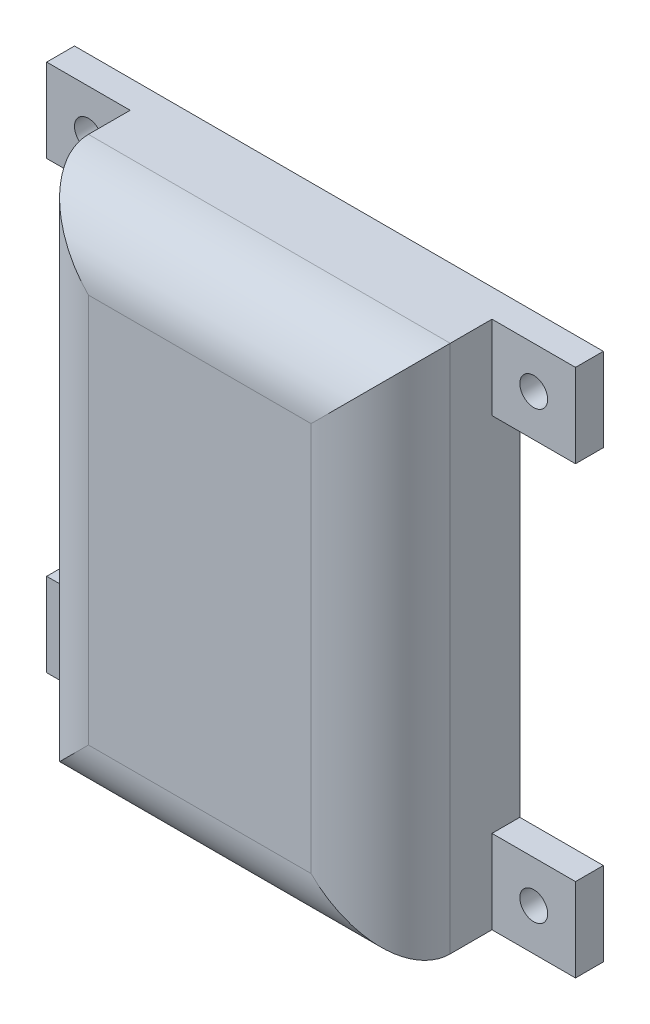
SolidWorks part; units mm, degrees
ref_plane "正面" through (0, 0, 0) normal (0, 0, 1) x (1, 0, 0)
ref_plane "平面" through (0, 0, 0) normal (0, 1, 0) x (1, 0, 0)
ref_plane "右側面" through (0, 0, 0) normal (1, 0, 0) x (0, 0, -1)
sketch "ｽｹｯﾁ1" plane through (0, 0, 0) normal (0, 0, 1) x (1, 0, 0)
  line L1 (13, -19) -> (-13, -19)
  line L2 (13, -19) -> (13, 19)
  line L3 (13, 19) -> (-13, 19)
  line L4 (-13, -19) -> (-13, 19)
  line L5 (13, -19) -> (-13, 19) construction
  line L6 (13, 19) -> (-13, -19) construction
  point P0 (0, 0)
  dimension "D1" = 38
  dimension "D2" = 26
extrude "ﾎﾞｽ - 押し出し1" add sketch "ｽｹｯﾁ1" along normal blind 10
sketch "ｽｹｯﾁ2" plane through (0, 0, 0) normal (0, 0, 1) x (1, 0, 0)
  line L1 (11, -17) -> (-11, -17)
  line L2 (11, -17) -> (11, 17)
  line L3 (11, 17) -> (-11, 17)
  line L4 (-11, -17) -> (-11, 17)
  line L5 (11, -17) -> (-11, 17) construction
  line L6 (11, 17) -> (-11, -17) construction
  point P0 (0, 0)
  dimension "D1" = 22
  dimension "D2" = 34
extrude "ｶｯﾄ - 押し出し1" cut sketch "ｽｹｯﾁ2" along normal blind 8
sketch "ｽｹｯﾁ3" plane through (0, 0, 0) normal (0, 0, 1) x (1, 0, 0)
  line L0 (13, 19) -> (-13, 19) construction
  line L1 (-0.8522, 2) -> (1.1478, 2)
  line L2 (-0.8522, 2) -> (-0.8522, 9)
  line L3 (-0.8522, 9) -> (1.1478, 9)
  line L4 (1.1478, 2) -> (1.1478, 9)
  line L5 (-0.8522, 2) -> (1.1478, 9) construction
  line L6 (-0.8522, 9) -> (1.1478, 2) construction
  point P0 (0.1478, 5.5)
  dimension "D1" = 7
  dimension "D2" = 2
  dimension "D3" = 10
sketch "ｽｹｯﾁ4" plane through (0, 0, 0) normal (0, 0, 1) x (1, 0, 0)
  line L0 (13, -19) -> (13, 19) construction
  line L1 (13, 19) -> (19, 19)
  line L2 (13, 19) -> (13, 13)
  line L3 (13, 13) -> (19, 13)
  line L4 (19, 19) -> (19, 13)
  line L5 (13, -19) -> (19, -19)
  line L6 (13, -19) -> (13, -13)
  line L7 (13, -13) -> (19, -13)
  line L8 (19, -19) -> (19, -13)
  line L9 (-13, -19) -> (13, -19) construction
  line L10 (-13, -19) -> (-19, -19)
  line L11 (-13, -19) -> (-13, -13)
  line L12 (-13, -13) -> (-19, -13)
  line L13 (-19, -19) -> (-19, -13)
  line L14 (-13, 19) -> (-19, 19)
  line L15 (-13, 19) -> (-13, 13)
  line L16 (-13, 13) -> (-19, 13)
  line L17 (-19, 19) -> (-19, 13)
  dimension "D1" = 6
  dimension "D2" = 6
  dimension "D3" = 6
  dimension "D4" = 6
  dimension "D5" = 6
  dimension "D6" = 6
  dimension "D7" = 6
  dimension "D8" = 6
  dimension "D9" = 0
extrude "ﾎﾞｽ - 押し出し2" add sketch "ｽｹｯﾁ4" along normal blind 2
sketch "ｽｹｯﾁ5" plane through (0, 0, 0) normal (0, 0, 1) x (1, 0, 0)
  line L0 (-13, 19) -> (-19, 19) construction
  line L1 (-19, 19) -> (-19, 13) construction
  line L2 (-13, -13) -> (-19, -13) construction
  line L3 (19, -19) -> (19, -13) construction
  line L4 (-19, -13) -> (-19, -19) construction
  line L5 (19, -13) -> (13, -13) construction
  line L6 (19, 13) -> (19, 19) construction
  line L7 (19, 19) -> (13, 19) construction
  circle A0 centre (-16, 16) radius 1
  circle A1 centre (-16, -16) radius 1
  circle A2 centre (16, -16) radius 1
  circle A3 centre (16, 16) radius 1
  dimension "D1" = 3
  dimension "D2" = 3
  dimension "D3" = 3
  dimension "D4" = 2
  dimension "D5" = 2
  dimension "D6" = 3
  dimension "D7" = 2
  dimension "D8" = 2
  dimension "D9" = 3
  dimension "D10" = 3
  dimension "D11" = 3
  dimension "D12" = 3
extrude "ｶｯﾄ - 押し出し4" cut sketch "ｽｹｯﾁ5" along normal blind 2
fillet "ﾌｨﾚｯﾄ1" radius 5 4 edges at (0, 19, 10) (0, -19, 10) (13, 0, 10) (-13, 0, 10)
